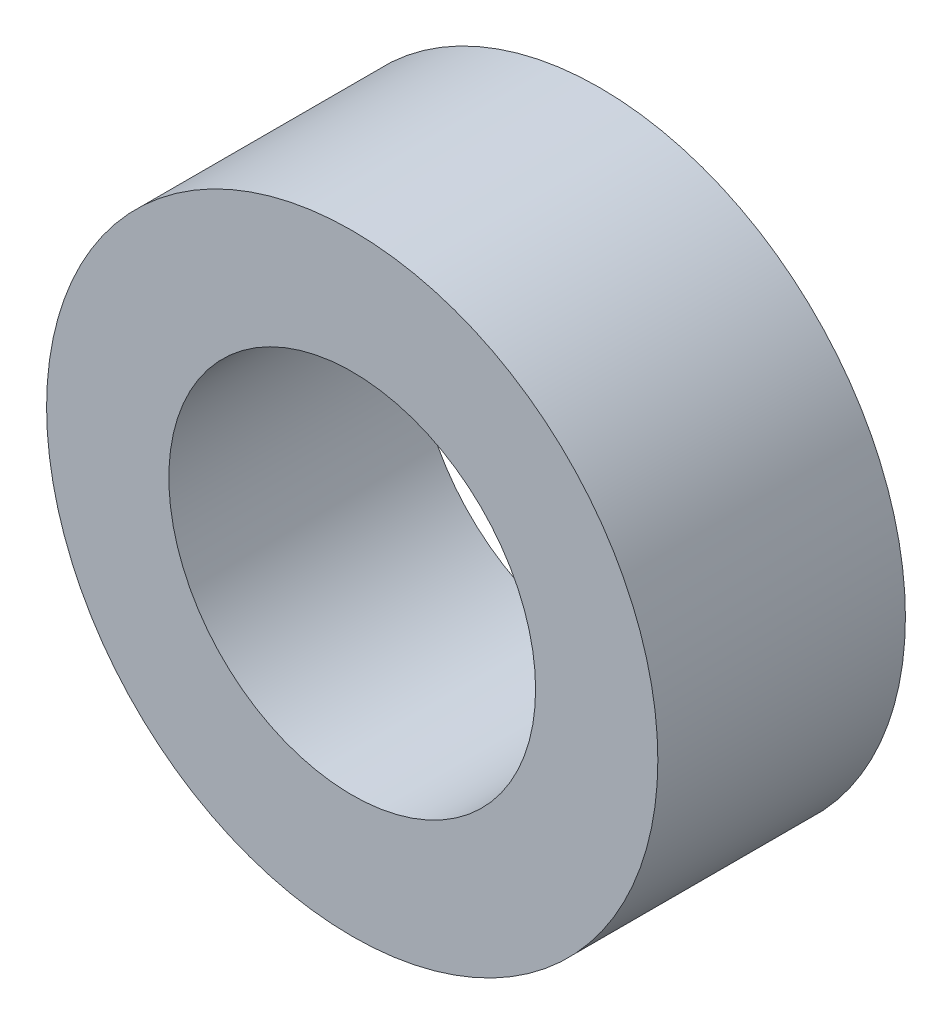
SolidWorks part; units mm, degrees
ref_plane "Front Plane" through (0, 0, 0) normal (0, 0, 1) x (1, 0, 0)
ref_plane "Top Plane" through (0, 0, 0) normal (0, 1, 0) x (1, 0, 0)
ref_plane "Right Plane" through (0, 0, 0) normal (1, 0, 0) x (0, 0, -1)
sketch "Sketch1" plane through (0, 0, 0) normal (0, 0, 1) x (1, 0, 0)
  circle A0 centre (0, 0) radius 12.7
  circle A2 centre (0, 0) radius 7.62
extrude "Boss-Extrude1" add sketch "Sketch1" along normal blind 10.287
